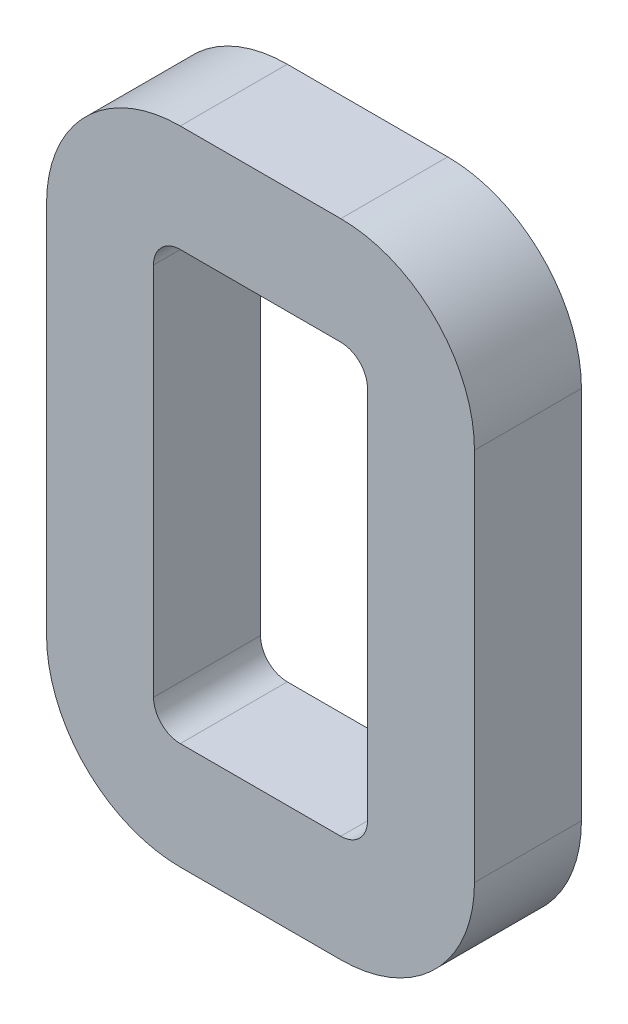
SolidWorks part; units mm, degrees
ref_plane "Front Plane" through (0, 0, 0) normal (0, 0, 1) x (1, 0, 0)
ref_plane "Top Plane" through (0, 0, 0) normal (0, 1, 0) x (1, 0, 0)
ref_plane "Right Plane" through (0, 0, 0) normal (1, 0, 0) x (0, 0, -1)
sketch "Sketch2" plane through (0, 0, 0) normal (0, 0, 1) x (1, 0, 0)
  line L0 (-12.7, 3.175) -> (-12.7, 47.625)
  line L1 (3.175, 0) -> (22.225, 0)
  line L2 (0, 3.175) -> (0, 47.625)
  line L3 (3.175, 50.8) -> (22.225, 50.8)
  line L4 (25.4, 3.175) -> (25.4, 47.625)
  line L5 (3.175, 63.5) -> (22.225, 63.5)
  line L6 (38.1, 3.175) -> (38.1, 47.625)
  line L7 (3.175, -12.7) -> (22.225, -12.7)
  arc A0 (0, 3.175) -> (3.175, 0) centre (3.175, 3.175) ccw
  arc A1 (22.225, 0) -> (25.4, 3.175) centre (22.225, 3.175) ccw
  arc A2 (22.225, 50.8) -> (25.4, 47.625) centre (22.225, 47.625) cw
  arc A3 (3.175, 50.8) -> (0, 47.625) centre (3.175, 47.625) ccw
  arc A4 (3.175, 63.5) -> (-12.7, 47.625) centre (3.175, 47.625) ccw
  arc A5 (22.225, 63.5) -> (38.1, 47.625) centre (22.225, 47.625) cw
  arc A6 (22.225, -12.7) -> (38.1, 3.175) centre (22.225, 3.175) ccw
  arc A7 (-12.7, 3.175) -> (3.175, -12.7) centre (3.175, 3.175) ccw
  point P7 (0, 0)
  dimension "D1" = 3.175
  dimension "D2" = 12.7
extrude "Boss-Extrude1" add sketch "Sketch2" along normal blind 12.7
